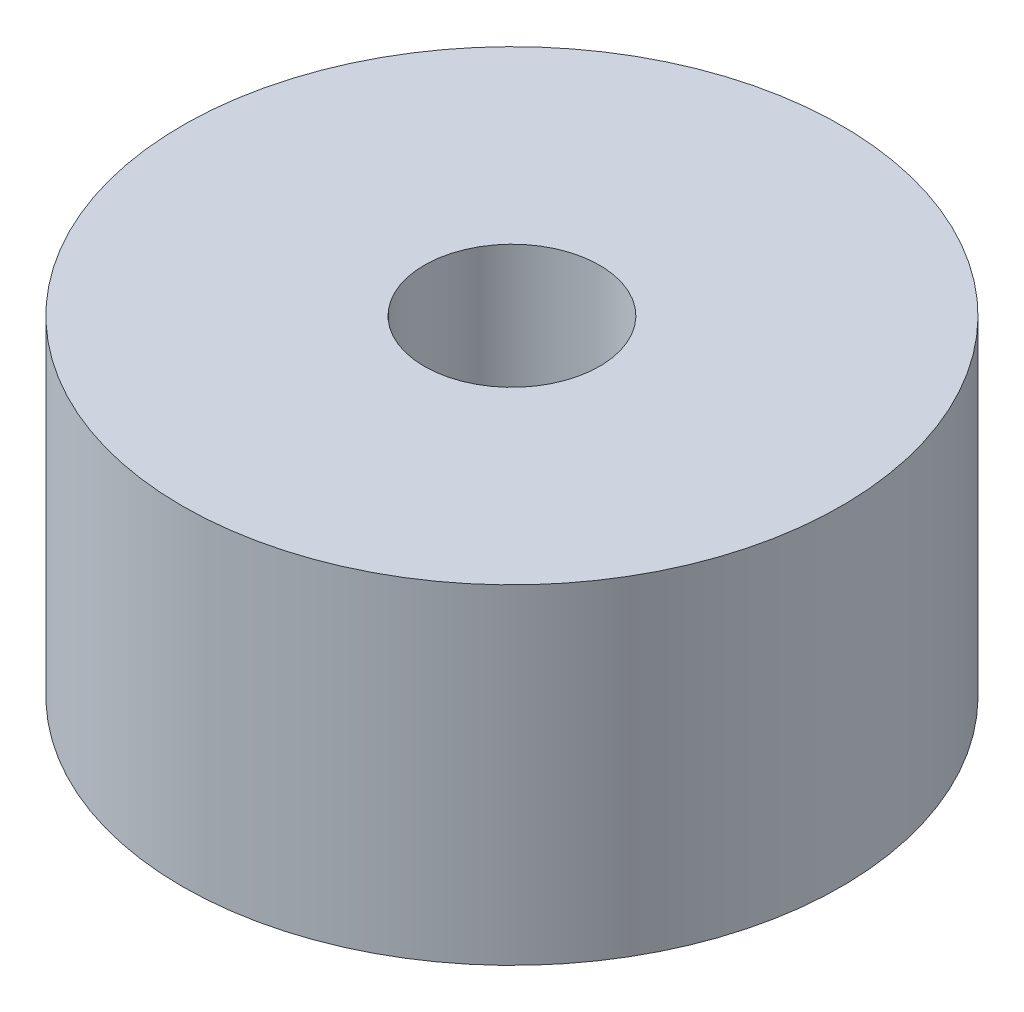
SolidWorks part; units mm, degrees
ref_plane "Front" through (0, 0, 0) normal (0, 0, 1) x (1, 0, 0)
ref_plane "Top" through (0, 0, 0) normal (0, 1, 0) x (1, 0, 0)
ref_plane "Right" through (0, 0, 0) normal (1, 0, 0) x (0, 0, -1)
sketch "Sketch1" plane through (0, 0, 0) normal (0, 1, 0) x (1, 0, 0)
  circle A0 centre (0, 0) radius 6.35
  circle A1 centre (0, 0) radius 1.6891
  dimension "D1" = 12.7
  dimension "D2" = 3.3782
extrude "Boss-Extrude1" add sketch "Sketch1" along normal blind 6.35
